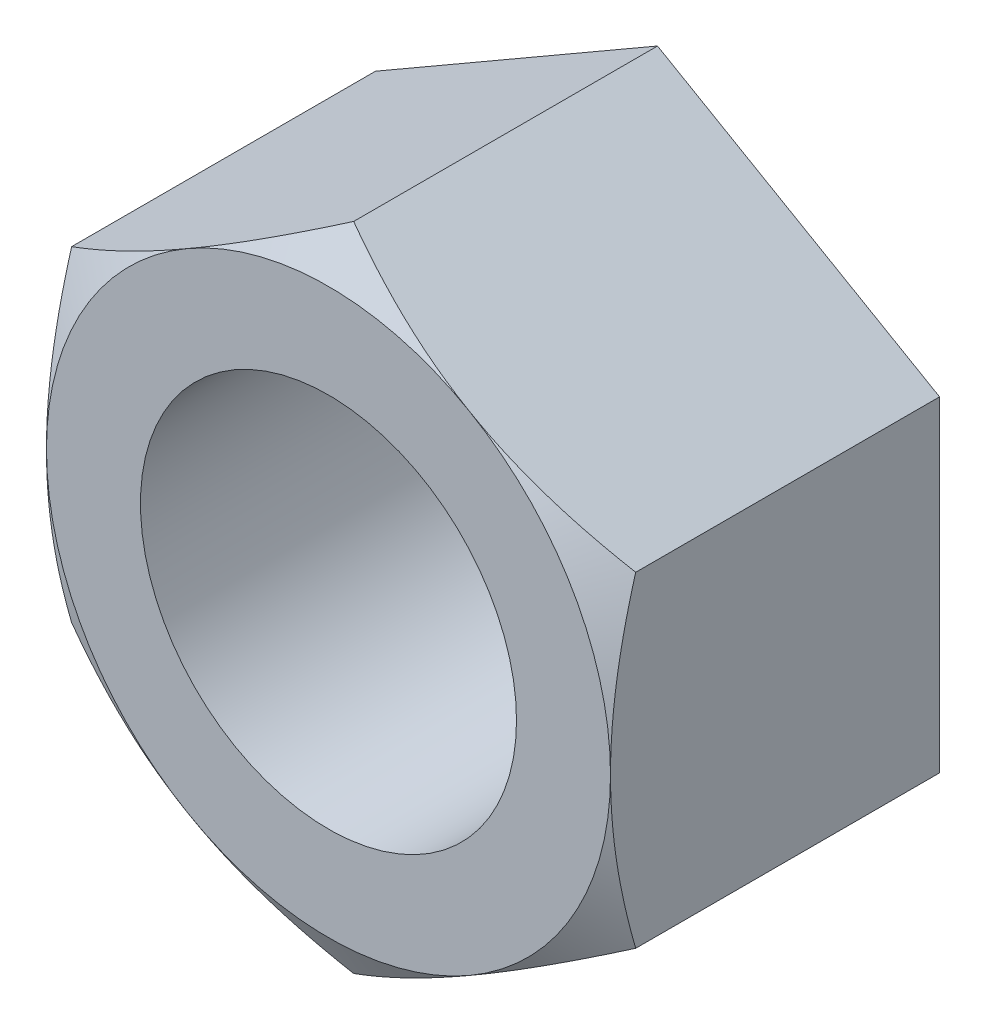
SolidWorks part; units mm, degrees
ref_plane "Front" through (0, 0, 0) normal (0, 0, 1) x (1, 0, 0)
ref_plane "Top" through (0, 0, 0) normal (0, 1, 0) x (1, 0, 0)
ref_plane "Right" through (0, 0, 0) normal (1, 0, 0) x (0, 0, -1)
sketch "Sketch1" plane through (0, 0, 0) normal (0, 0, 1) x (1, 0, 0)
  line L1 (-11.9062, 6.8741) -> (-11.9062, -6.8741)
  line L2 (-11.9062, -6.8741) -> (0, -13.7482)
  line L3 (0, -13.7482) -> (11.9063, -6.8741)
  line L4 (11.9063, -6.8741) -> (11.9063, 6.8741)
  line L5 (11.9063, 6.8741) -> (0, 13.7482)
  line L6 (0, 13.7482) -> (-11.9062, 6.8741)
  circle A0 centre (0, 0) radius 11.9062 construction
  circle A1 centre (0, 0) radius 7.9375
  point P10 (0, 7.9375)
  dimension "hex" = 23.8125
  dimension "dia" = 15.875
extrude "Extrude1" add sketch "Sketch1" along normal mid plane 13.8906
sketch "Sketch4" plane through (0, 0, -6.9453) normal (0, 0, -1) x (-1, 0, 0)
  circle A0 centre (0, 0) radius 7.9375 construction
  circle A1 centre (0, 0) radius 7.9375
curve "Helix/Spiral3" pitch 2.3091 height 16.6687 turns 7.2188
sketch "Sketch3" plane through (0, 0, 0) normal (1, 0, 0) x (0, 0, -1)
  line L0 (6.9453, 7.9375) -> (8.9658, 7.9375)
  line L1 (8.9658, 7.9375) -> (8.0999, 6.4377)
  line L2 (8.0999, 6.4377) -> (7.8112, 6.4377)
  line L3 (7.8112, 6.4377) -> (6.9453, 7.9375)
  line L4 (7.3783, 7.1876) -> (8.5328, 7.1876) construction
  dimension "D1" = 60
  dimension "D2" = 1.1545
  dimension "D3" = 0.2886
sketch "Sketch7" plane through (0, 0, 6.9453) normal (0, 0, 1) x (1, 0, 0)
  circle A0 centre (0, 0) radius 11.9062 construction
  circle A1 centre (0, 0) radius 11.9062
extrude "Extrude2" cut sketch "Sketch7" against normal blind 25.4 draft 60 flip side to cut
equation "\"D3@Helix/Spiral3\" = \"length@Extrude1\" * 1.2"
equation "\"D2@Sketch3\" = \"D4@Helix/Spiral3\" * .5"
equation "\"D3@Sketch3\" = \"D4@Helix/Spiral3\" * .125"
